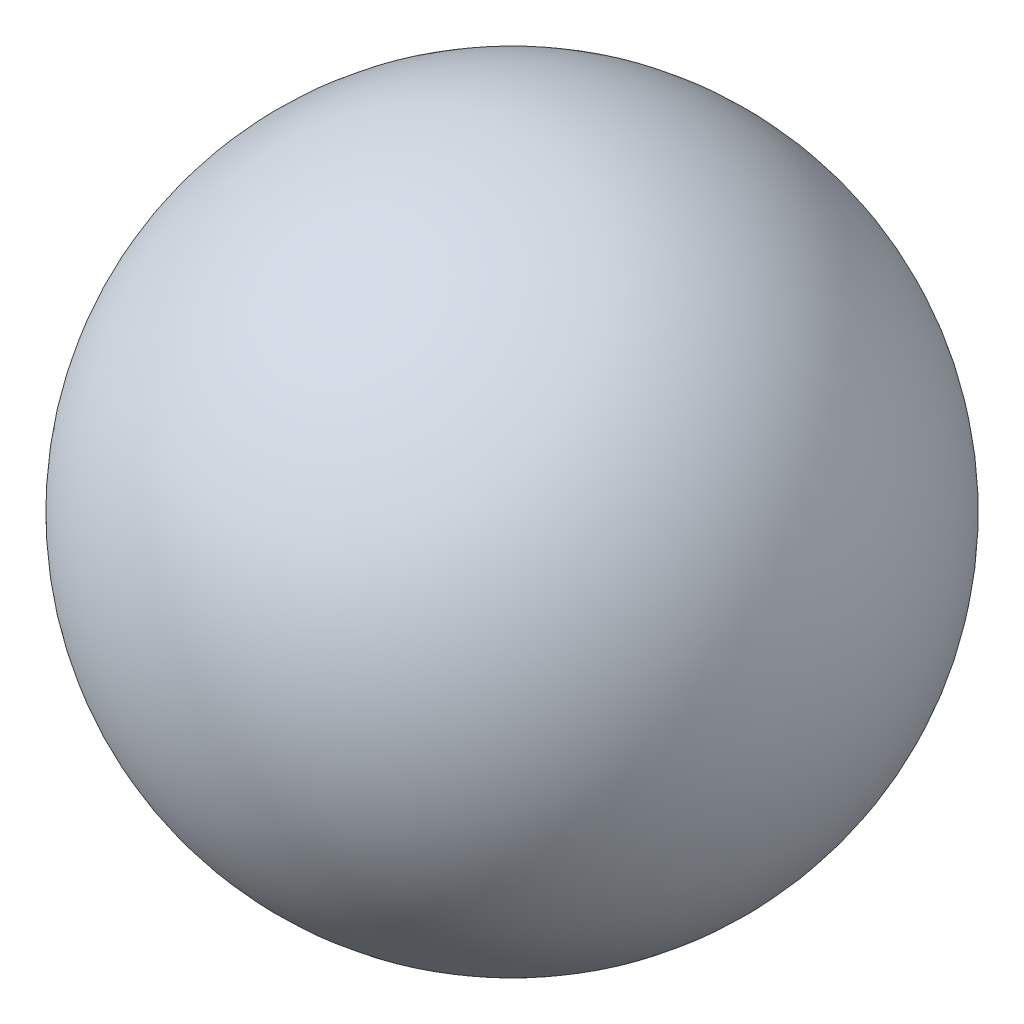
SolidWorks part; units mm, degrees
ref_plane "Plan de face" through (0, 0, 0) normal (0, 0, 1) x (1, 0, 0)
ref_plane "Plan de dessus" through (0, 0, 0) normal (0, 1, 0) x (1, 0, 0)
ref_plane "Plan de droite" through (0, 0, 0) normal (1, 0, 0) x (0, 0, -1)
sketch "Esquisse2" plane through (0, 0, 0) normal (0, 0, 1) x (1, 0, 0)
  line L0 (0, 32.5) -> (0, -32.5)
  line L1 (0, 43.7383) -> (0, -44.2641) construction
  arc A0 (0, 32.5) -> (0, -32.5) centre (0, 0) cw
  dimension "D1" = 32.5
revolve "Révolution1" add sketch "Esquisse2" angle 360 about L1
